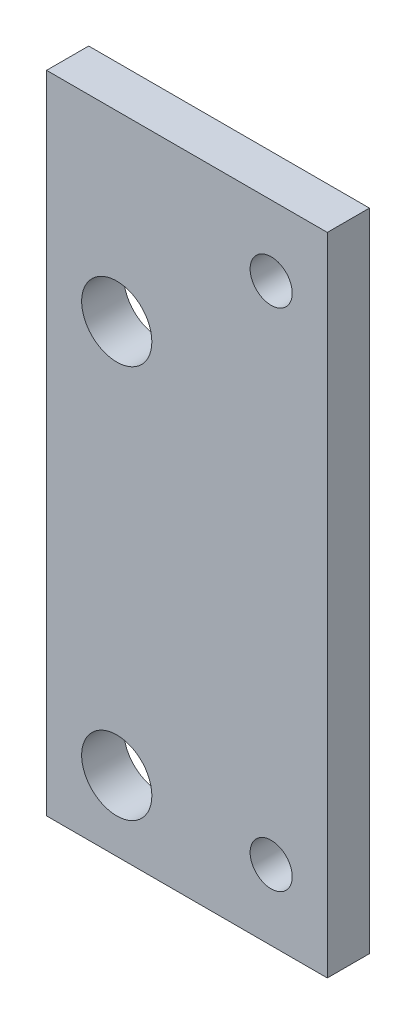
SolidWorks part; units mm, degrees
ref_plane "Face" through (0, 0, 0) normal (0, 0, 1) x (1, 0, 0)
ref_plane "Dessus" through (0, 0, 0) normal (0, 1, 0) x (1, 0, 0)
ref_plane "Droite" through (0, 0, 0) normal (1, 0, 0) x (0, 0, -1)
sketch "Esquisse1" plane through (0, 0, 0) normal (0, 0, 1) x (1, 0, 0)
  line L0 (5, 46) -> (5, 0) construction
  line L1 (0, 0) -> (20, 0)
  line L2 (0, 0) -> (0, 46)
  line L3 (0, 46) -> (20, 46)
  line L4 (20, 0) -> (20, 46)
  line L5 (16, 46) -> (16, 0) construction
  line L6 (20, 23) -> (0, 23) construction
  circle A0 centre (5, 33) radius 2.5
  circle A1 centre (5, 5) radius 2.5
  circle A2 centre (16, 41) radius 1.5
  circle A3 centre (16, 5) radius 1.5
  dimension "D6" = 5
  dimension "D7" = 33
  dimension "D8" = 3
  dimension "D1" = 20
  dimension "D2" = 46
  dimension "D3" = 5
  dimension "D4" = 4
  dimension "D5" = 5
  dimension "D9" = 5
extrude "Extrusion1" add sketch "Esquisse1" along normal blind 3
